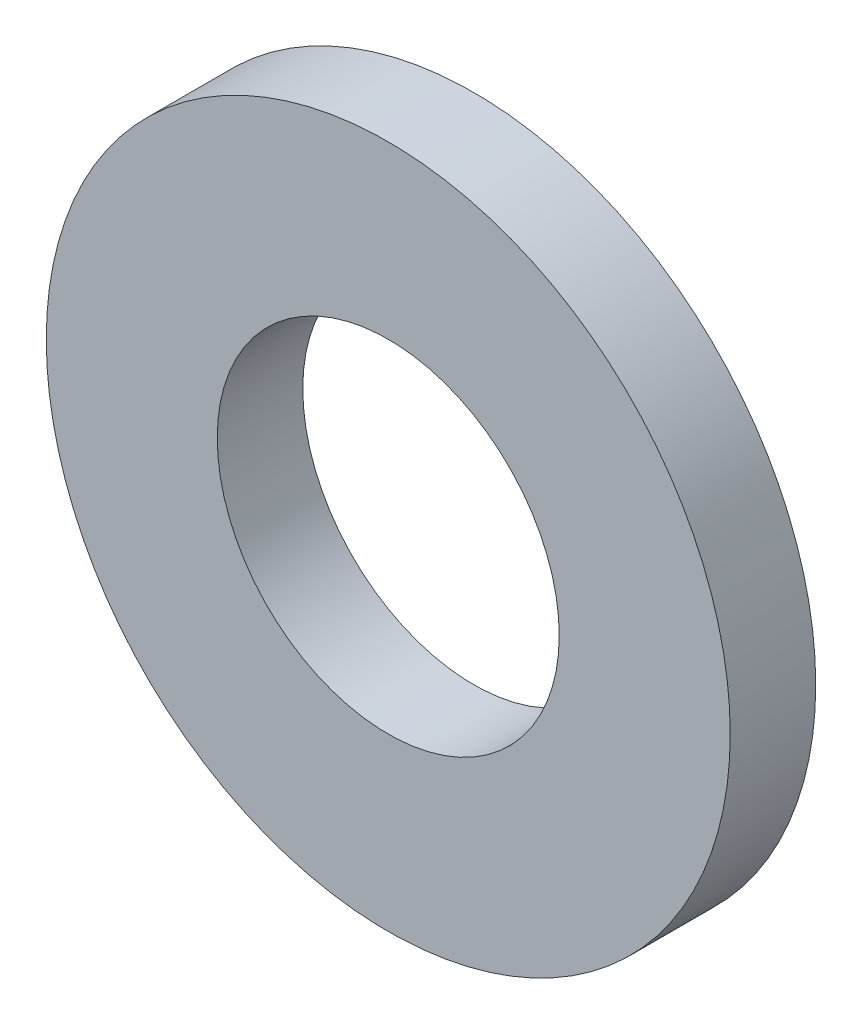
SolidWorks part; units mm, degrees
material "Plain Carbon Steel"
ref_plane "Front Plane" through (0, 0, 0) normal (0, 0, 1) x (1, 0, 0)
ref_plane "Top Plane" through (0, 0, 0) normal (0, 1, 0) x (1, 0, 0)
ref_plane "Right Plane" through (0, 0, 0) normal (1, 0, 0) x (0, 0, -1)
sketch "Sketch2" plane through (0, 0, 0) normal (0, 0, 1) x (1, 0, 0)
  circle A0 centre (0, 0) radius 8
  circle A1 centre (0, 0) radius 4
  dimension "D1" = 16
  dimension "D2" = 8
extrude "Boss-Extrude1" add sketch "Sketch2" along normal blind 2
